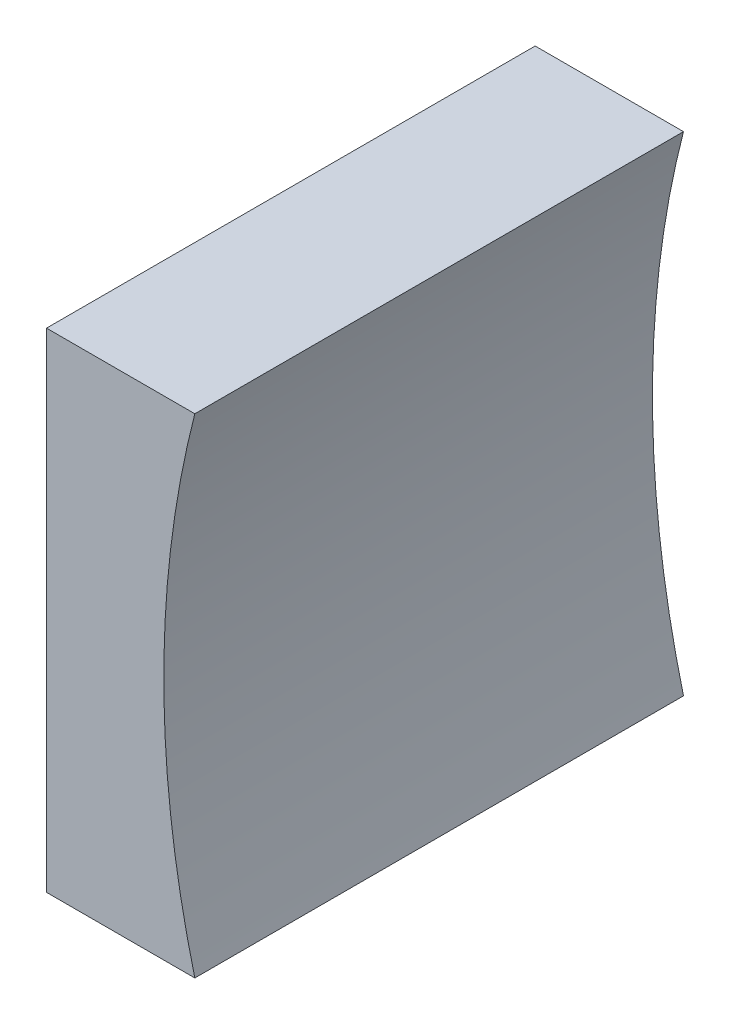
SolidWorks part; units mm, degrees
ref_plane "前视基准面" through (0, 0, 0) normal (0, 0, 1) x (1, 0, 0)
ref_plane "上视基准面" through (0, 0, 0) normal (0, 1, 0) x (1, 0, 0)
ref_plane "右视基准面" through (0, 0, 0) normal (1, 0, 0) x (0, 0, -1)
sketch "草图1" plane through (0, 0, 0) normal (0, 0, 1) x (1, 0, 0)
  line L0 (278.655, 66.8579) -> (298.183, 66.8579) construction
  line L1 (284.7071, 66.8579) -> (284.7071, 79.3579)
  line L2 (284.7071, 79.3579) -> (292.2948, 79.3579)
  line L3 (292.2948, 54.3579) -> (284.7071, 54.3579)
  line L4 (284.7071, 54.3579) -> (284.7071, 66.8579)
  arc A0 (292.2948, 79.3579) -> (292.2948, 54.3579) centre (340.7071, 66.8579) ccw
  dimension "D1" = 50
  dimension "D2" = 7.5877
extrude "凸台-拉伸1" add sketch "草图1" along normal blind 25
